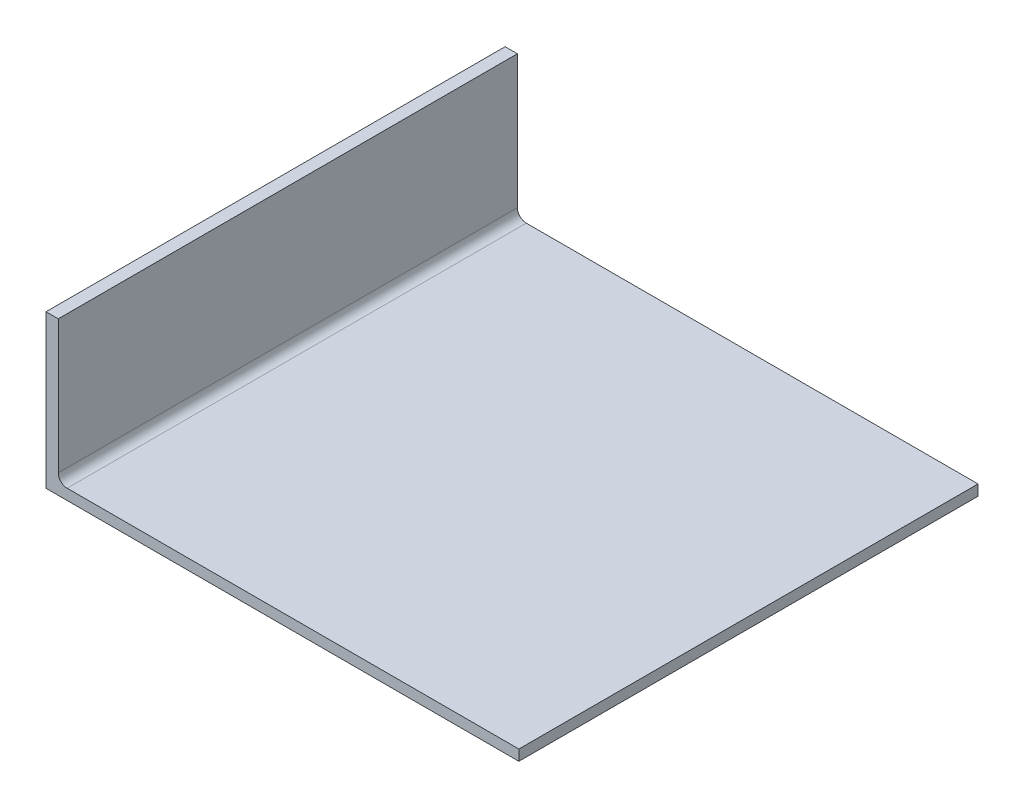
SolidWorks part; units mm, degrees
ref_plane "Front Plane" through (0, 0, 0) normal (0, 0, 1) x (1, 0, 0)
ref_plane "Top Plane" through (0, 0, 0) normal (0, 1, 0) x (1, 0, 0)
ref_plane "Right Plane" through (0, 0, 0) normal (1, 0, 0) x (0, 0, -1)
sketch "Sketch1" plane through (0, 0, 0) normal (0, 1, 0) x (1, 0, 0)
  line L1 (3.8179, 21.2243) -> (-262.1325, 21.2243)
  line L2 (3.8179, 21.2243) -> (3.8179, -236.9969)
  line L3 (3.8179, -236.9969) -> (-262.1325, -236.9969)
  line L6 (-262.1325, 21.2243) -> (-262.1325, -236.9969)
extrude "Base" add sketch "Sketch1" along normal blind 6
sketch "Sketch2" plane through (0, 6, 0) normal (0, 1, 0) x (1, 0, 0)
  line L0 (-262.1325, -236.9969) -> (3.8179, -236.9969) construction
  line L1 (-262.1325, 21.2243) -> (-255.2403, 21.2243)
  line L2 (-262.1325, 21.2243) -> (-262.1325, -236.9969)
  line L3 (-262.1325, -236.9969) -> (-255.2403, -236.9969)
  line L4 (-255.2403, 21.2243) -> (-255.2403, -236.9969)
extrude "Boss-Extrude2" add sketch "Sketch2" along normal blind 80
fillet "Fillet1" radius 5 1 edges at (-255.2403, 6, 107.8863)
